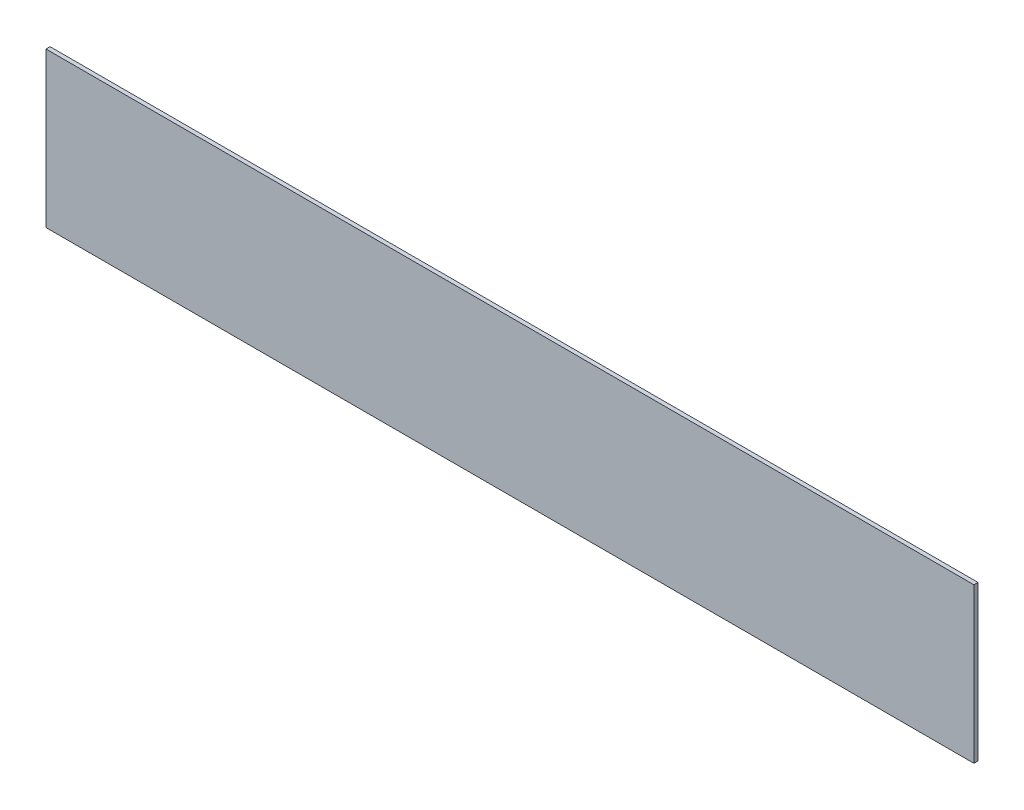
SolidWorks part; units mm, degrees
material "Стекло"
ref_plane "Спереди" through (0, 0, 0) normal (0, 0, 1) x (1, 0, 0)
ref_plane "Сверху" through (0, 0, 0) normal (0, 1, 0) x (1, 0, 0)
ref_plane "Справа" through (0, 0, 0) normal (1, 0, 0) x (0, 0, -1)
sketch "Эскиз1" plane through (0, 0, 0) normal (0, 0, 1) x (1, 0, 0)
  line L1 (-228.6, 38.1) -> (228.6, 38.1)
  line L2 (-228.6, 38.1) -> (-228.6, -38.1)
  line L3 (-228.6, -38.1) -> (228.6, -38.1)
  line L4 (228.6, 38.1) -> (228.6, -38.1)
  line L5 (-228.6, 38.1) -> (228.6, -38.1) construction
  line L6 (-228.6, -38.1) -> (228.6, 38.1) construction
  point P0 (0, 0)
  dimension "D1" = 457.2
  dimension "D2" = 76.2
extrude "Бобышка-Вытянуть1" add sketch "Эскиз1" along normal blind 2
